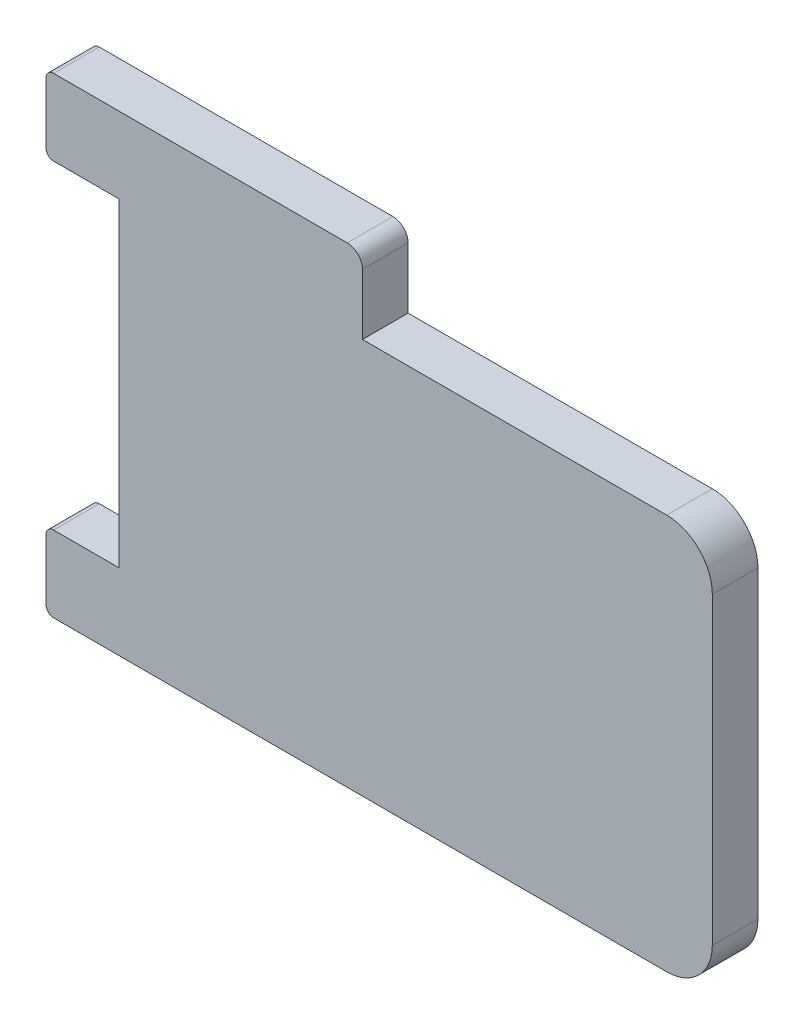
SolidWorks part; units mm, degrees
ref_plane "Спереди" through (0, 0, 0) normal (0, 0, 1) x (1, 0, 0)
ref_plane "Сверху" through (0, 0, 0) normal (0, 1, 0) x (1, 0, 0)
ref_plane "Справа" through (0, 0, 0) normal (1, 0, 0) x (0, 0, -1)
sketch "Эскиз1" plane through (0, 0, 0) normal (0, 0, 1) x (1, 0, 0)
  line L0 (-23.7277, 0) -> (-18.1585, 0) construction
  line L1 (-19.5, 15.5) -> (-4.5, 15.5)
  line L2 (-19.5, 15.5) -> (-19.5, -15.5)
  line L3 (-19.5, -15.5) -> (16.5, -15.5)
  line L4 (19.5, 7.5) -> (19.5, -12.5)
  line L5 (-19.5, 15.5) -> (19.5, -15.5) construction
  line L6 (-19.5, -15.5) -> (19.5, 15.5) construction
  line L7 (-24.3, 15.5) -> (-19.5, 15.5)
  line L8 (-24.3, 15.5) -> (-24.3, 10.5)
  line L9 (-24.3, 10.5) -> (-19.5, 10.5)
  line L10 (-19.5, 15.5) -> (-19.5, 10.5)
  line L11 (-24.3, 15.5) -> (-19.5, 10.5) construction
  line L12 (-24.3, 10.5) -> (-19.5, 15.5) construction
  line L13 (-24.3, -10.5) -> (-19.5, -10.5)
  line L14 (-24.3, -10.5) -> (-24.3, -15.5)
  line L15 (-24.3, -15.5) -> (-19.5, -15.5)
  line L16 (-19.5, -10.5) -> (-19.5, -15.5)
  line L17 (-24.3, -10.5) -> (-19.5, -15.5) construction
  line L18 (-24.3, -15.5) -> (-19.5, -10.5) construction
  line L19 (-3.5, 14.5) -> (-3.5, 10.5)
  line L20 (-3.5, 10.5) -> (16.5, 10.5)
  arc A0 (16.5, -15.5) -> (19.5, -12.5) centre (16.5, -12.5) ccw
  arc A2 (-4.5, 15.5) -> (-3.5, 14.5) centre (-4.5, 14.5) cw
  arc A3 (19.5, 7.5) -> (16.5, 10.5) centre (16.5, 7.5) ccw
  point P0 (0, 0)
  point P5 (-21.9, 13)
  point P10 (-21.9, -13)
  point P26 (-3.5, 15.5)
  point P29 (19.5, 10.5)
  dimension "D5" = 3
  dimension "D8" = 1
  dimension "D9" = 3
  dimension "D1" = 5
  dimension "D2" = 26
  dimension "D3" = 4.8
  dimension "D4" = 39
  dimension "D6" = 23
  dimension "5" = 5
extrude "Бобышка-Вытянуть1" add sketch "Эскиз1" along normal blind 3
fillet "Скругление1" radius 0.5 4 edges at (-24.3, -15.5, 1.5) (-24.3, -10.5, 1.5) (-24.3, 10.5, 1.5) (-24.3, 15.5, 1.5)
